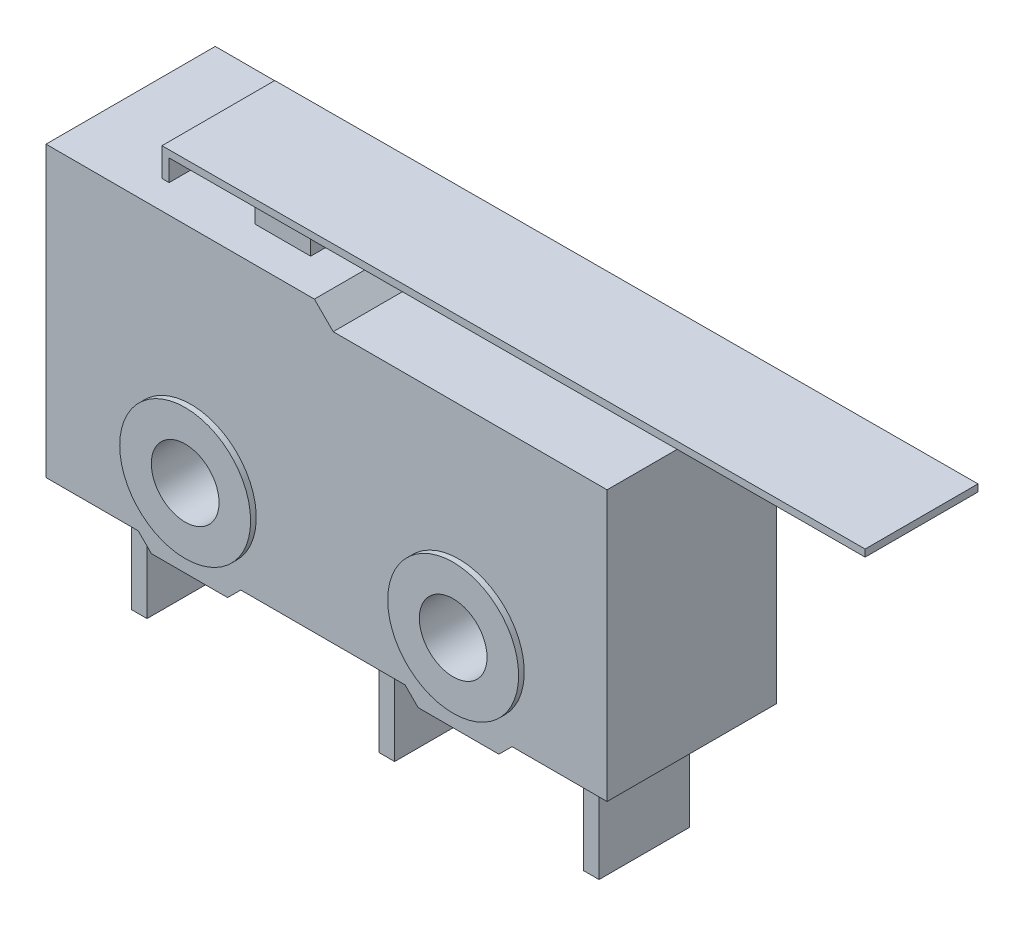
SolidWorks part; units mm, degrees
ref_plane "Front Plane" through (0, 0, 0) normal (0, 0, 1) x (1, 0, 0)
ref_plane "Top Plane" through (0, 0, 0) normal (0, 1, 0) x (1, 0, 0)
ref_plane "Right Plane" through (0, 0, 0) normal (1, 0, 0) x (0, 0, -1)
sketch "Sketch2" plane through (0, 0, 0) normal (0, 0, 1) x (1, 0, 0)
  line L0 (-5.0429, -2.5053) -> (14.7571, -2.5053) construction
  line L1 (55, 0) -> (-55, 0) construction
  line L2 (-5.1329, -2.4988) -> (-1.8634, -2.4988)
  line L3 (-5.1329, -2.4988) -> (-5.1329, 7.7372)
  line L4 (-5.1329, 7.7372) -> (4.3799, 7.7372)
  line L5 (14.7551, -2.4988) -> (14.7551, 7.0697)
  line L6 (14.7551, 7.0697) -> (5.0475, 7.0697)
  line L7 (5.0475, 7.0697) -> (4.3799, 7.7372)
  line L8 (-1.8634, -2.4988) -> (-1.3977, -2.9645)
  line L9 (-1.3977, -2.9645) -> (1.3048, -2.9645)
  line L10 (1.3048, -2.9645) -> (1.7705, -2.4988)
  line L11 (7.5948, -2.4988) -> (8.0605, -2.9645)
  line L12 (8.0605, -2.9645) -> (10.9207, -2.9645)
  line L13 (10.9207, -2.9645) -> (11.3864, -2.4988)
  line L14 (11.3864, -2.4988) -> (14.7551, -2.4988)
  line L15 (1.7705, -2.4988) -> (7.5948, -2.4988)
  circle A0 centre (0, 0) radius 1.2
  circle A1 centre (9.5, 0) radius 1.2
  dimension "D2" = 2.4
  dimension "D3" = 2.4
  dimension "D4" = 9.5
  dimension "D1" = 19.8
extrude "Boss-Extrude1" add sketch "Sketch2" along normal mid plane 6
sketch "Sketch3" plane through (0, 0, 0) normal (0, 0, 1) x (1, 0, 0)
  circle A0 centre (0, 0) radius 1.2 construction
  circle A1 centre (0, 0) radius 1.2
  circle A2 centre (9.5, 0) radius 1.2 construction
  circle A3 centre (9.5, 0) radius 1.2
  circle A4 centre (0, 0) radius 2.3196
  circle A5 centre (9.5, 0) radius 2.3196
extrude "Boss-Extrude2" add sketch "Sketch3" along normal mid plane 6.4
sketch "Sketch5" plane through (0, 0, 0) normal (0, 0, 1) x (1, 0, 0)
  line L0 (-1.8903, 6.4393) -> (-1.8974, 8.6201)
  line L1 (-1.8974, 8.6201) -> (22.9025, 8.7012)
  line L2 (0, -44.7868) -> (0, 44.7868) construction
  line L3 (55, 0) -> (-55, 0) construction
  line L4 (11.3864, -2.4988) -> (14.7551, -2.4988) construction
  dimension "D1" = 24.8
  dimension "D2" = 1.8903
  dimension "D3" = 6.4393
  dimension "D4" = 11.2
  dimension "D5" = 2.1808
extrude "Extrude-Thin1" add sketch "Sketch5" along normal mid plane 4 separate body thin thin type mid plane wall 0.25
sketch "Sketch4" plane through (0, 0, 0) normal (0, 0, 1) x (1, 0, 0)
  line L0 (1.019, 7.7372) -> (1.019, 8.5046)
  line L1 (-5.1329, 7.7372) -> (4.3799, 7.7372) construction
  line L2 (1.019, 7.7372) -> (2.9988, 7.7372)
  line L3 (2.9988, 8.5111) -> (2.9988, 7.7372)
  line L4 (-1.772, 8.4955) -> (22.9029, 8.5762) construction
  line L5 (1.019, 8.5046) -> (2.9988, 8.5111)
extrude "Boss-Extrude3" add sketch "Sketch4" along normal mid plane 3.5
sketch "Sketch6" plane through (0, 0, 0) normal (0, 0, 1) x (1, 0, 0)
  line L0 (-5.1329, -2.4988) -> (-1.8634, -2.4988) construction
  line L1 (-3.4982, -2.4988) -> (-2.9517, -2.4988)
  line L2 (-3.4982, -2.4988) -> (-3.4982, -6.4378)
  line L3 (-3.4982, -6.4378) -> (-2.9517, -6.4378)
  line L4 (-2.9517, -2.4988) -> (-2.9517, -6.4378)
  line L5 (1.7705, -2.4988) -> (7.5948, -2.4988) construction
  line L6 (5.2791, -2.4988) -> (5.8255, -2.4988)
  line L7 (5.2791, -2.4988) -> (5.2791, -6.4378)
  line L8 (5.2791, -6.4378) -> (5.8255, -6.4378)
  line L9 (5.8255, -2.4988) -> (5.8255, -6.4378)
  line L10 (11.3864, -2.4988) -> (14.7551, -2.4988) construction
  line L11 (12.5243, -2.4988) -> (13.0707, -2.4988)
  line L12 (12.5243, -2.4988) -> (12.5243, -6.4378)
  line L13 (12.5243, -6.4378) -> (13.0707, -6.4378)
  line L14 (13.0707, -2.4988) -> (13.0707, -6.4378)
extrude "Boss-Extrude4" add sketch "Sketch6" along normal mid plane 3.2 separate body
